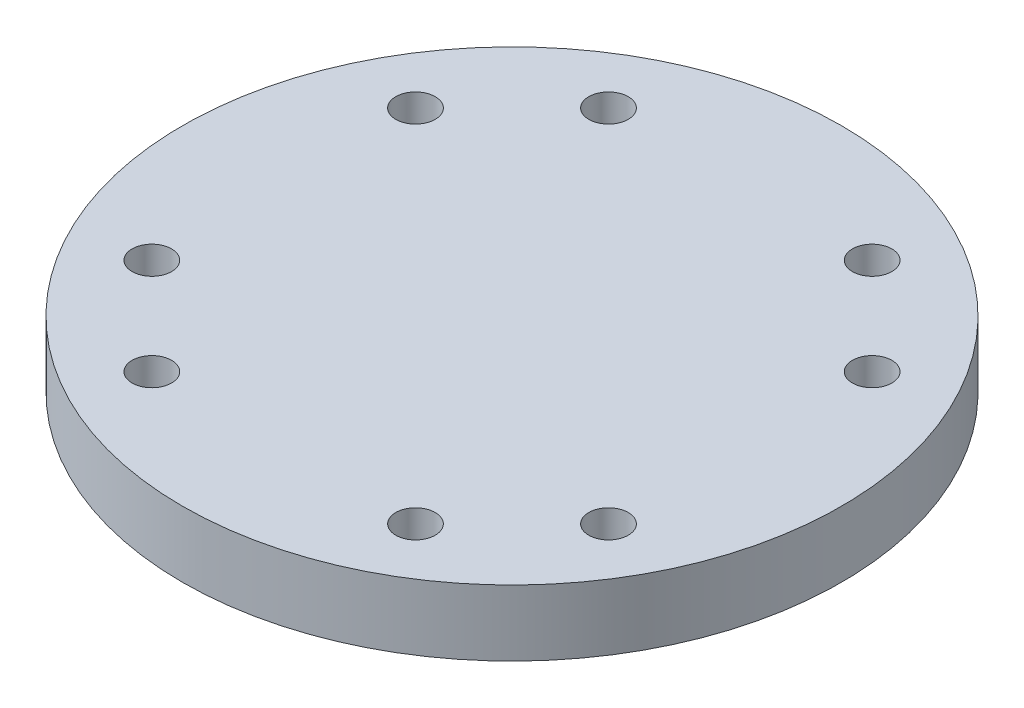
SolidWorks part; units mm, degrees
ref_plane "Front Plane" through (0, 0, 0) normal (0, 0, 1) x (1, 0, 0)
ref_plane "Top Plane" through (0, 0, 0) normal (0, 1, 0) x (1, 0, 0)
ref_plane "Right Plane" through (0, 0, 0) normal (1, 0, 0) x (0, 0, -1)
sketch "Sketch1" plane through (0, 0, 0) normal (0, 1, 0) x (1, 0, 0)
  line L0 (21.997, 12.7) -> (0, 0) construction
  line L1 (0, 0) -> (60.5217, 0) construction
  circle A0 centre (0, 0) radius 31.75
  circle A1 centre (21.997, 12.7) radius 1.9
  circle A3 centre (21.997, -12.7) radius 1.9
  circle A4 centre (-12.7, -21.997) radius 1.9
  circle A5 centre (12.7, -21.997) radius 1.9
  circle A6 centre (-21.997, 12.7) radius 1.9
  circle A7 centre (-21.997, -12.7) radius 1.9
  circle A8 centre (12.7, 21.997) radius 1.9
  circle A9 centre (-12.7, 21.997) radius 1.9
  point P23 (0, 0)
  dimension "D1" = 63.5
  dimension "D3" = 3.8
  dimension "D2" = 30
  dimension "D4" = 25.4
  dimension "D5" = 4
extrude "Boss-Extrude1" add sketch "Sketch1" along normal mid plane 6.35
equation "\"D3@Sketch1\"=3.8mm"
